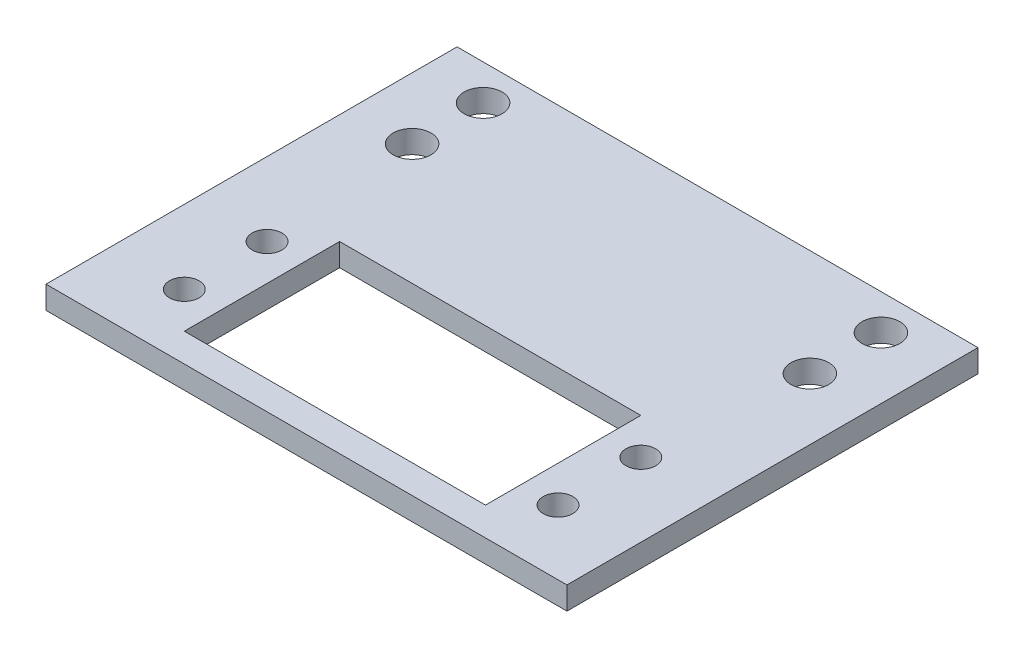
SolidWorks part; units mm, degrees
material "6061 Alloy"
ref_plane "Front Plane" through (0, 0, 0) normal (0, 0, 1) x (1, 0, 0)
ref_plane "Top Plane" through (0, 0, 0) normal (0, 1, 0) x (1, 0, 0)
ref_plane "Center plane" through (0, 0, 0) normal (1, 0, 0) x (0, 0, -1)
sketch "Sketch1" plane through (0, 0, 0) normal (0, 1, 0) x (1, 0, 0)
  line L0 (-16.2537, 0) -> (0, 0) construction
  line L1 (-20.193, -10.414) -> (20.193, -10.414)
  line L2 (-20.193, -10.414) -> (-20.193, 10.414)
  line L3 (-20.193, 10.414) -> (20.193, 10.414)
  line L4 (20.193, -10.414) -> (20.193, 10.414)
  line L5 (-20.193, -10.414) -> (20.193, 10.414) construction
  line L6 (-20.193, 10.414) -> (20.193, -10.414) construction
  line L7 (0, 0) -> (0, 13.3077) construction
  line L8 (0, 40.894) -> (0, -14.224) construction
  line L9 (-34.925, 40.894) -> (34.925, 40.894)
  line L10 (-34.925, 40.894) -> (-34.925, -14.224)
  line L11 (-34.925, -14.224) -> (34.925, -14.224)
  line L12 (34.925, 40.894) -> (34.925, -14.224)
  line L13 (0, 45.3335) -> (-26.67, 45.3335) construction
  line L14 (-26.67, 45.3335) -> (-26.67, 36.1315) construction
  line L15 (-26.67, 36.1315) -> (-26.67, 26.6065) construction
  line L16 (0, 45.3335) -> (0, 40.894) construction
  circle A0 centre (-25.0571, -5.5499) radius 1.9875
  circle A1 centre (-25.0571, 5.5499) radius 1.9875
  circle A2 centre (25.0571, -5.5499) radius 1.9875
  circle A3 centre (25.0571, 5.5499) radius 1.9875
  circle A4 centre (-26.67, 36.1315) radius 2.54
  circle A5 centre (-26.67, 26.6065) radius 2.54
  circle A6 centre (26.67, 26.6065) radius 2.54
  circle A7 centre (26.67, 36.1315) radius 2.54
  point P0 (0, 0)
  dimension "D3" = 3.9751
  dimension "D10" = 5.08
  dimension "D1" = 4.8641
  dimension "D2" = 4.8641
  dimension "D4" = 40.386
  dimension "D5" = 20.828
  dimension "D6" = 69.85
  dimension "D7" = 55.118
  dimension "D8" = 3.81
  dimension "D9" = 26.67
  dimension "D11" = 9.525
  dimension "D12" = 4.7625
extrude "Boss-Extrude1" add sketch "Sketch1" along normal blind 3.048
equation "\"D12@Sketch1\"=(0.75-0.375)/2"
